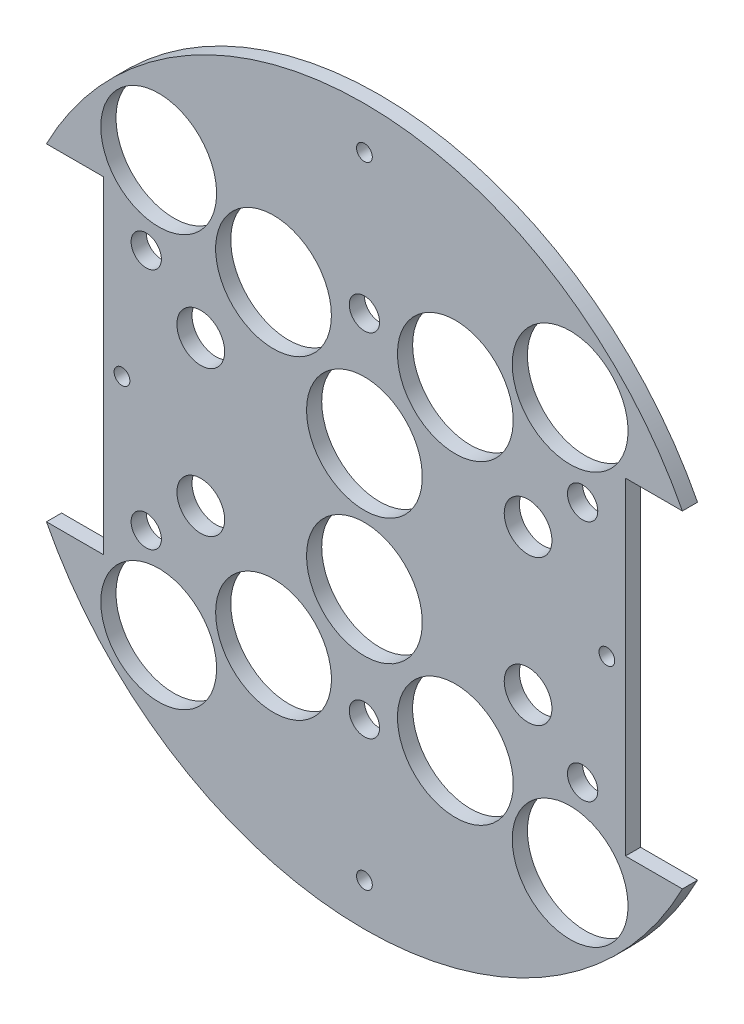
SolidWorks part; units mm, degrees
ref_plane "Front Plane" through (0, 0, 0) normal (0, 0, 1) x (1, 0, 0)
ref_plane "Top Plane" through (0, 0, 0) normal (0, 1, 0) x (1, 0, 0)
ref_plane "Right Plane" through (0, 0, 0) normal (1, 0, 0) x (0, 0, -1)
sketch "Sketch1" plane through (0, 0, 0) normal (0, 0, 1) x (1, 0, 0)
  line L0 (0, 0) -> (-82.1241, 0) construction
  line L1 (0, 0) -> (0, 95.6219) construction
  line L3 (-66.6236, 34.29) -> (-54.6856, 34.29)
  line L5 (-66.6236, -34.29) -> (-54.6856, -34.29)
  line L6 (-54.6856, 34.29) -> (-54.6856, -34.29)
  line L7 (66.6236, -34.29) -> (54.6856, -34.29)
  line L8 (66.6236, 34.29) -> (54.6856, 34.29)
  line L9 (54.6856, 34.29) -> (54.6856, -34.29)
  arc A0 (-66.6236, -34.29) -> (66.6236, -34.29) centre (0, 0) ccw
  circle A1 centre (-45.466, 11.049) radius 1.651
  circle A2 centre (-20.0673, 10.795) radius 1.651
  circle A3 centre (-20.0673, -10.795) radius 1.651
  circle A4 centre (-45.466, -11.049) radius 1.651
  circle A5 centre (45.466, -11.049) radius 1.651
  circle A6 centre (20.0673, -10.795) radius 1.651
  circle A7 centre (20.0673, 10.795) radius 1.651
  circle A8 centre (45.466, 11.049) radius 1.651
  arc A9 (66.6236, 34.29) -> (-66.6236, 34.29) centre (0, 0) ccw
  dimension "D2" = 3.302
  dimension "D3" = 3.302
  dimension "D4" = 25.4
  dimension "D5" = 10.795
  dimension "D10" = 45.466
  dimension "D6" = 68.58
  dimension "D7" = 11.938
  dimension "D8" = 74.93
  dimension "D9" = 74.93
  dimension "D11" = 34.29
extrude "Boss-Extrude2" add sketch "Sketch1" along normal blind 3.175
sketch "Sketch3" plane through (0, 0, 0) normal (0, 0, -1) x (-1, 0, 0)
  line L0 (0, 0) -> (0, -116.2908) construction
  line L1 (0, 0) -> (-153.8039, 0) construction
  line L2 (0, 0) -> (15.2681, -56.9814) construction
  line L3 (0, 0) -> (15.2302, -26.3795) construction
  circle A1 centre (0, -13.208) radius 12.1285
  circle A2 centre (0, 13.208) radius 12.1285
  circle A4 centre (-43.1052, -43.1052) radius 12.1285
  circle A6 centre (19.05, -32.9956) radius 12.1285
  circle A7 centre (19.05, 32.9956) radius 12.1285
  circle A8 centre (-43.1052, 43.1052) radius 12.1285
  circle A11 centre (43.1052, 43.1052) radius 12.1285
  circle A12 centre (-19.05, 32.9956) radius 12.1285
  circle A13 centre (-19.05, -32.9956) radius 12.1285
  circle A14 centre (43.1052, -43.1052) radius 12.1285
  point P36 (0, 0)
  point P53 (0, 0)
  point P55 (0, 0)
  dimension "D1" = 24.257
  dimension "D2" = 24.257
  dimension "D4" = 15
  dimension "D6" = 0
  dimension "D8" = 24.257
  dimension "D9" = 30
  dimension "D10" = 13.208
  dimension "D11" = 13.208
extrude "Cut-Extrude2" cut sketch "Sketch3" against normal through all
sketch "Sketch4" plane through (0, 0, 0) normal (0, 0, -1) x (-1, 0, 0)
  line L1 (51.5324, -18.4451) -> (14.45, -18.4451)
  line L2 (51.5324, -18.4451) -> (51.5324, 15.6028)
  line L3 (51.5324, 15.6028) -> (14.45, 15.6028)
  line L4 (14.45, -18.4451) -> (14.45, 15.6028)
  line L5 (-15.5728, -16.8859) -> (-52.5974, -16.8859)
  line L6 (-15.5728, -16.8859) -> (-15.5728, 15.6028)
  line L7 (-15.5728, 15.6028) -> (-52.5974, 15.6028)
  line L8 (-52.5974, -16.8859) -> (-52.5974, 15.6028)
extrude "Boss-Extrude3" add sketch "Sketch4" against normal up to surface (3.175 mm away) up to face at (-55.2337, 43.1052, 3.175)
sketch "Sketch5" plane through (0, 0, 0) normal (0, 0, -1) x (-1, 0, 0)
  line L0 (0, 0) -> (51.3983, 0) construction
  line L1 (0, 0) -> (0, -30.9946) construction
  circle A0 centre (34.29, -15.24) radius 5
  circle A1 centre (-34.29, -15.24) radius 5
  circle A2 centre (34.29, 15.24) radius 5
  circle A3 centre (-34.29, 15.24) radius 5
  dimension "D1" = 10
  dimension "D2" = 10
  dimension "D3" = 10
  dimension "D4" = 10
  dimension "D5" = 30.48
  dimension "D6" = 68.58
  dimension "D7" = 30.48
  dimension "D8" = 68.58
extrude "Cut-Extrude3" cut sketch "Sketch5" against normal through all
extrude "Cut-Extrude4" cut sketch "Sketch6" against normal through all both and the other way through all
sketch "Sketch6" plane through (31.3134, -132.614, 3.175) normal (0, 0, 1) x (0, -1, 0)
  line L0 (-132.614, -31.3134) -> (-132.614, 57.8454) construction
  line L1 (-132.614, -31.3134) -> (-222.516, -31.3134) construction
  circle A0 centre (-158.014, 14.4066) radius 3.175
  circle A1 centre (-169.444, -31.3134) radius 3.175
  circle A3 centre (-158.014, -77.0334) radius 3.175
  circle A4 centre (-107.214, -77.0334) radius 3.175
  circle A5 centre (-95.784, -31.3134) radius 3.175
  circle A6 centre (-107.214, 14.4066) radius 3.175
extrude "Cut-Extrude5" cut sketch "Sketch7" against normal blind 16.51
sketch "Sketch7" plane through (31.3134, -132.614, 15.875) normal (0, 0, 1) x (0, -1, 0)
  line L0 (-132.614, -31.3134) -> (-132.614, -98.8476) construction
  line L1 (-132.614, -31.3134) -> (-20.2053, -31.3134) construction
  circle A1 centre (-198.654, -31.3134) radius 1.651
  circle A2 centre (-66.574, -31.3134) radius 1.651
  circle A3 centre (-132.614, -82.1134) radius 1.651
  circle A4 centre (-132.614, 19.4866) radius 1.651
